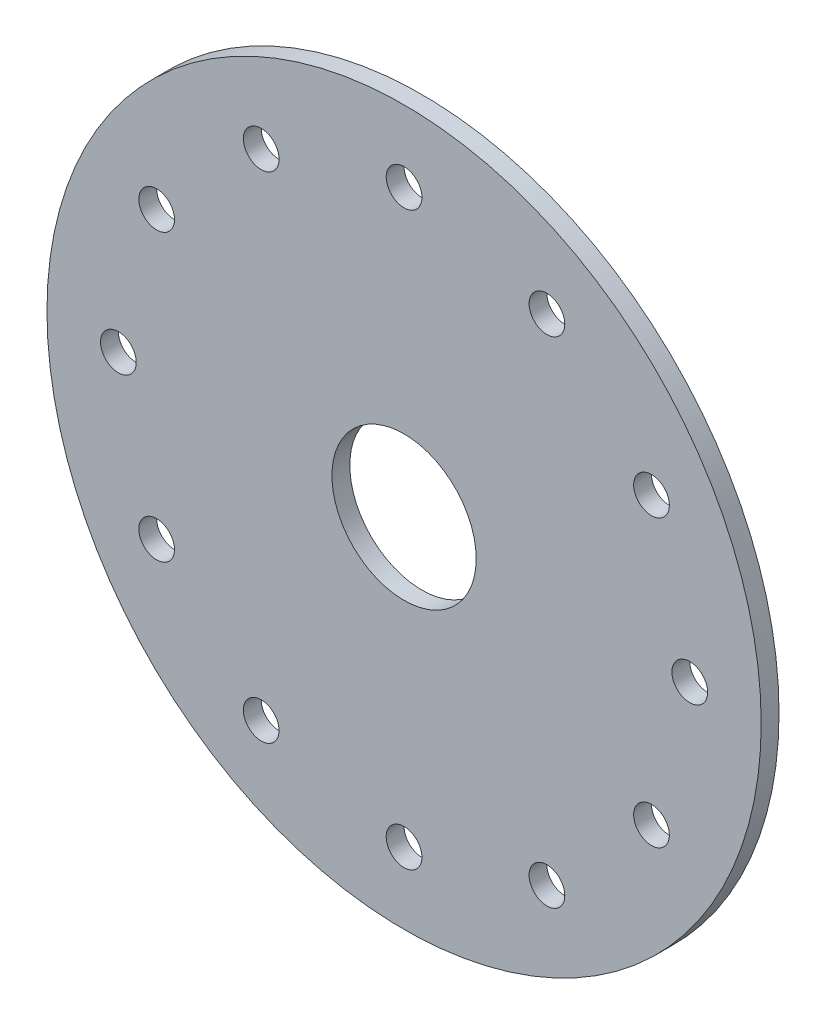
SolidWorks part; units mm, degrees
ref_plane "Front Plane" through (0, 0, 0) normal (0, 0, 1) x (1, 0, 0)
ref_plane "Top Plane" through (0, 0, 0) normal (0, 1, 0) x (1, 0, 0)
ref_plane "Right Plane" through (0, 0, 0) normal (1, 0, 0) x (0, 0, -1)
sketch "Sketch1" plane through (0, 0, 0) normal (0, 0, 1) x (1, 0, 0)
  line L0 (-90.8107, 34.654) -> (-90.8107, 60.054) construction
  circle A0 centre (-90.8107, 34.654) radius 31.75
  circle A1 centre (-90.8107, 34.654) radius 25.4 construction
  circle A2 centre (-90.8107, 60.054) radius 1.5875
  circle A3 centre (-78.1107, 56.651) radius 1.5875
  circle A4 centre (-68.8137, 47.354) radius 1.5875
  circle A5 centre (-65.4107, 34.654) radius 1.5875
  circle A6 centre (-68.8137, 21.954) radius 1.5875
  circle A7 centre (-78.1107, 12.6569) radius 1.5875
  circle A8 centre (-90.8107, 9.254) radius 1.5875
  circle A9 centre (-103.5107, 12.6569) radius 1.5875
  circle A10 centre (-112.8078, 21.954) radius 1.5875
  circle A11 centre (-116.2107, 34.654) radius 1.5875
  circle A12 centre (-112.8078, 47.354) radius 1.5875
  circle A13 centre (-103.5107, 56.651) radius 1.5875
  circle A14 centre (-90.8107, 34.654) radius 6.4135
  point P27 (-90.8107, 34.654)
  dimension "D1" = 63.5
  dimension "D2" = 50.8
  dimension "D3" = 3.175
  dimension "D4" = 12.827
extrude "Boss-Extrude1" add sketch "Sketch1" along normal blind 1.5875
